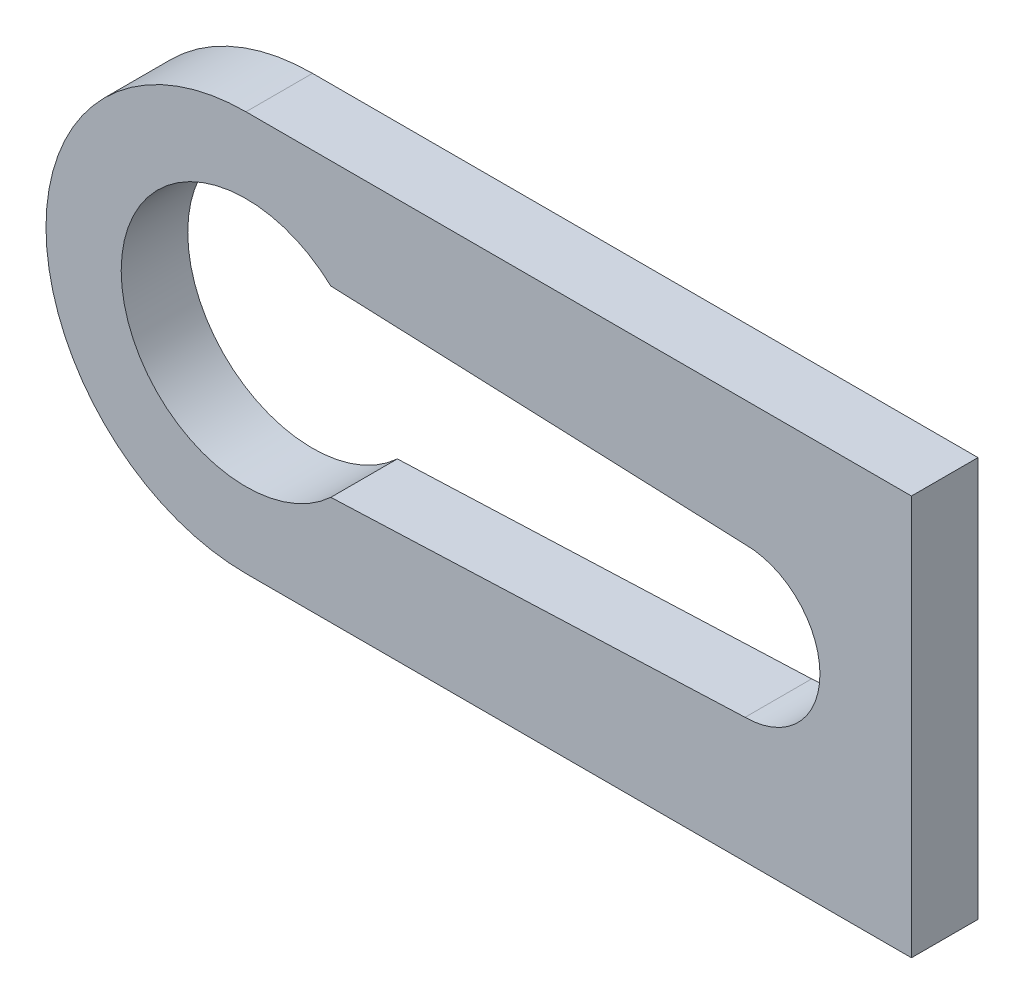
SolidWorks part; units mm, degrees
ref_plane "Front Plane" through (0, 0, 0) normal (0, 0, 1) x (1, 0, 0)
ref_plane "Top Plane" through (0, 0, 0) normal (0, 1, 0) x (1, 0, 0)
ref_plane "Right Plane" through (0, 0, 0) normal (1, 0, 0) x (0, 0, -1)
sketch "Sketch1" plane through (0, 0, 0) normal (0, 0, 1) x (1, 0, 0)
  line L0 (-15, 0) -> (15, 0) construction
  line L1 (-15, 6.0098) -> (15, 6.0098)
  line L2 (-15, -6.0098) -> (15, -6.0098)
  line L3 (-15, -9.7865) -> (-15, 9.7865) construction
  line L6 (5, 6.0098) -> (5, -6.0098)
  line L7 (0, -10.0228) -> (0, 10.0228) construction
  line L8 (-12.4505, 2.75) -> (0, 2.25)
  line L9 (-12.4505, -2.75) -> (0, -2.25)
  line L10 (-12.4505, 2.75) -> (-12.4505, -2.75)
  circle A0 centre (-15, 0) radius 1
  arc A1 (-15, 6.0098) -> (-15, -6.0098) centre (-15, 0) ccw
  arc A2 (15, -6.0098) -> (15, 6.0098) centre (15, 0) ccw
  circle A3 centre (15, 0) radius 1
  circle A6 centre (-15, 0) radius 3.75
  circle A7 centre (0, 0) radius 2.25
  point P0 (0, 0)
  point P4 (0, 0)
  point P21 (-15, 0)
  point P24 (0, 0)
  dimension "D1" = 2
  dimension "D3" = 6.0098
  dimension "D4" = 2
  dimension "D5" = 7.5
  dimension "D7" = 4.5
  dimension "D2" = 30
  dimension "D6" = 15
  dimension "D8" = 5.5
extrude "Boss-Extrude1" add sketch "Sketch1" along normal blind 2
